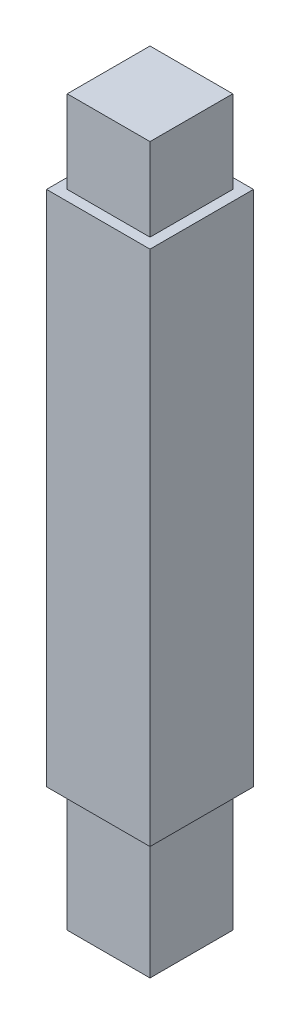
SolidWorks part; units mm, degrees
ref_plane "Front Plane" through (0, 0, 0) normal (0, 0, 1) x (1, 0, 0)
ref_plane "Top Plane" through (0, 0, 0) normal (0, 1, 0) x (1, 0, 0)
ref_plane "Right Plane" through (0, 0, 0) normal (1, 0, 0) x (0, 0, -1)
sketch "Sketch1" plane through (0, 0, 0) normal (0, 0, 1) x (1, 0, 0)
  line L1 (0, 0) -> (12.7, 0)
  line L2 (0, 0) -> (0, 63.5)
  line L3 (0, 63.5) -> (12.7, 63.5)
  line L4 (12.7, 0) -> (12.7, 63.5)
  dimension "D1" = 63.5
  dimension "D2" = 12.7
extrude "Boss-Extrude1" add sketch "Sketch1" along normal blind 12.7
sketch "Sketch2" plane through (0, 63.5, 0) normal (0, 1, 0) x (1, 0, 0)
  line L0 (0, -12.7) -> (0, 0) construction
  line L1 (1.27, -1.27) -> (11.43, -1.27)
  line L2 (1.27, -1.27) -> (1.27, -11.43)
  line L3 (1.27, -11.43) -> (11.43, -11.43)
  line L4 (11.43, -1.27) -> (11.43, -11.43)
  line L5 (12.7, -12.7) -> (0, -12.7) construction
  dimension "D1" = 10.16
  dimension "D2" = 10.16
  dimension "D3" = 1.27
  dimension "D4" = 1.27
extrude "Boss-Extrude2" add sketch "Sketch2" along normal blind 10.16
sketch "Sketch3" plane through (0, 0, 0) normal (0, -1, 0) x (1, 0, 0)
  line L0 (0, 12.7) -> (0, 0) construction
  line L1 (1.27, 11.43) -> (11.43, 11.43)
  line L2 (1.27, 11.43) -> (1.27, 1.27)
  line L3 (1.27, 1.27) -> (11.43, 1.27)
  line L4 (11.43, 11.43) -> (11.43, 1.27)
  line L5 (0, 0) -> (12.7, 0) construction
  dimension "D1" = 10.16
  dimension "D2" = 10.16
  dimension "D3" = 1.27
  dimension "D4" = 1.27
extrude "Boss-Extrude3" add sketch "Sketch3" along normal blind 15.24
